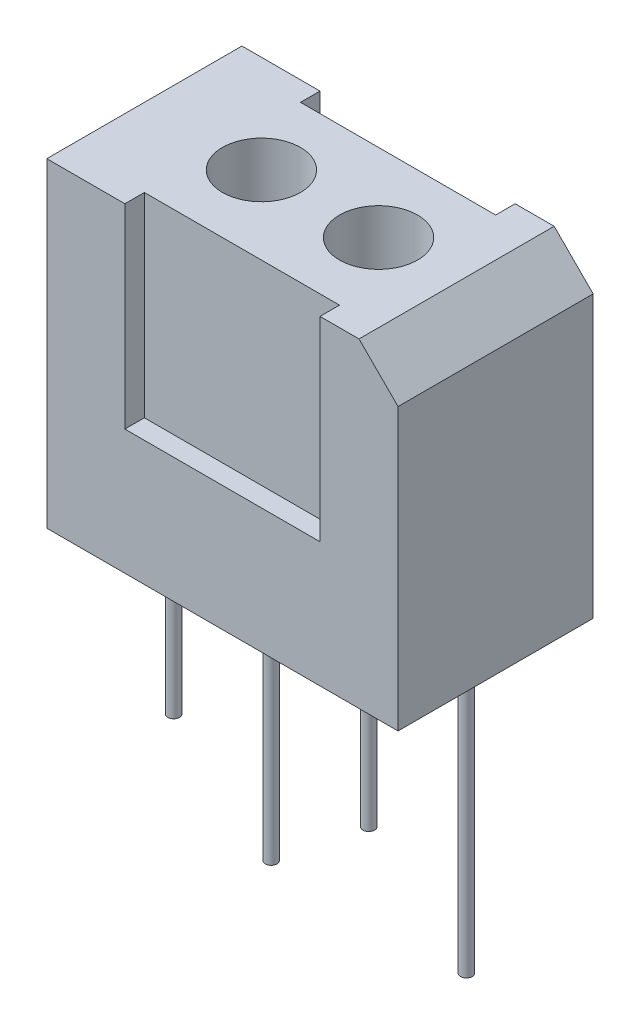
SolidWorks part; units mm, degrees
ref_plane "Front Plane" through (0, 0, 0) normal (0, 0, 1) x (1, 0, 0)
ref_plane "Top Plane" through (0, 0, 0) normal (0, 1, 0) x (1, 0, 0)
ref_plane "Right Plane" through (0, 0, 0) normal (1, 0, 0) x (0, 0, -1)
sketch "Sketch1" plane through (0, 0, 0) normal (0, 0, 1) x (1, 0, 0)
  line L1 (-4.5, 4.1) -> (4.5, 4.1)
  line L2 (-4.5, 4.1) -> (-4.5, -4.1)
  line L3 (-4.5, -4.1) -> (4.5, -4.1)
  line L4 (4.5, 4.1) -> (4.5, -4.1)
  line L5 (-4.5, 4.1) -> (4.5, -4.1) construction
  line L6 (-4.5, -4.1) -> (4.5, 4.1) construction
  point P0 (0, 0)
  dimension "D1" = 8.2
  dimension "D2" = 9
extrude "Boss-Extrude1" add sketch "Sketch1" along normal mid plane 5
chamfer "Chamfer1" distance 1 angle 45 1 edges at (4.5, 4.1, 0)
sketch "Sketch2" plane through (0, 4.1, 0) normal (0, 1, 0) x (1, 0, 0)
  line L0 (3.5, -2.5) -> (2.5, -2.5) construction
  line L1 (3.5, -2.5) -> (-4.5, -2.5) construction
  line L2 (-4.51, 0) -> (4.51, 0) construction
  line L3 (2.5, -2.5) -> (-2.5, -2.5)
  line L4 (2.5, -2.5) -> (2.5, -2)
  line L5 (2.5, -2) -> (-2.5, -2)
  line L6 (-2.5, -2.5) -> (-2.5, -2)
  line L7 (-2.5, 2.5) -> (-2.5, 2)
  line L8 (2.5, 2) -> (-2.5, 2)
  line L9 (2.5, 2.5) -> (2.5, 2)
  line L10 (2.5, 2.5) -> (-2.5, 2.5)
  dimension "D1" = 1
  dimension "D2" = 0.5
  dimension "D3" = 5
extrude "Cut-Extrude1" cut sketch "Sketch2" against normal blind 5
sketch "Sketch3" plane through (0, 4.1, 0) normal (0, 1, 0) x (1, 0, 0)
  line L0 (0, 0) -> (1.5, 0) construction
  line L1 (0, -2.75) -> (0, 2.75) construction
  circle A0 centre (1.5, 0) radius 1
  circle A1 centre (-1.5, 0) radius 1
  dimension "D2" = 2
  dimension "D1" = 1.5
extrude "Cut-Extrude2" cut sketch "Sketch3" against normal blind 2
sketch "Sketch4" plane through (0, -4.1, 0) normal (0, -1, 0) x (1, 0, 0)
  line L0 (0, 0) -> (1.25, 0) construction
  line L1 (0, 0) -> (-3.75, 0) construction
  circle A0 centre (1.25, 0) radius 0.15
  circle A1 centre (-3.75, 0) radius 0.15
  dimension "D2" = 0.3
  dimension "D4" = 0.3
  dimension "D1" = 1.25
  dimension "D3" = 3.75
extrude "Boss-Extrude2" add sketch "Sketch4" along normal blind 5
sketch "Sketch5" plane through (0, -4.1, 0) normal (0, -1, 0) x (1, 0, 0)
  line L0 (0, 0) -> (-1.25, 0) construction
  line L1 (0, 0) -> (3.75, 0) construction
  circle A0 centre (-1.25, 0) radius 0.15
  circle A1 centre (3.75, 0) radius 0.15
  dimension "D3" = 0.3
  dimension "D4" = 0.3
  dimension "D1" = 1.25
  dimension "D2" = 3.75
extrude "Boss-Extrude3" add sketch "Sketch5" along normal blind 7
